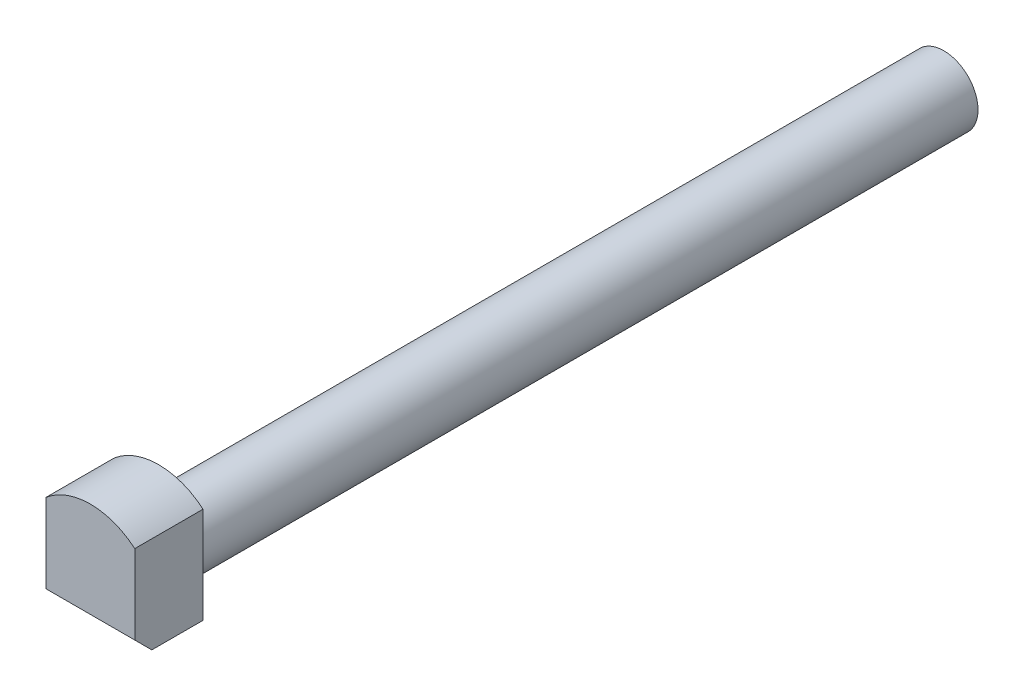
SolidWorks part; units mm, degrees
ref_plane "Plan de face" through (0, 0, 0) normal (0, 0, 1) x (1, 0, 0)
ref_plane "Plan de dessus" through (0, 0, 0) normal (0, 1, 0) x (1, 0, 0)
ref_plane "Plan de droite" through (0, 0, 0) normal (1, 0, 0) x (0, 0, -1)
sketch "Esquisse2" plane through (0, 0, 0) normal (0, 0, 1) x (1, 0, 0)
  circle A0 centre (0, 1.35) radius 1 construction
  circle A1 centre (0, 1.35) radius 1
extrude "Boss.-Extru.1" add sketch "Esquisse2" along normal blind 16.5 and the other way up to surface (11 mm away)
sketch "Esquisse3" plane through (0, 0, 16.5) normal (0, 0, 1) x (1, 0, 0)
  circle A0 centre (0, 1.35) radius 2
  dimension "D1" = 4
extrude "Boss.-Extru.2" add sketch "Esquisse3" along normal blind 2
sketch "Esquisse4" plane through (0, 0, 18.5) normal (0, 0, 1) x (1, 0, 0)
  line L0 (0, 1.35) -> (0, 4.5988) construction
  line L2 (-1.3, 2.8699) -> (-1.3, 0.05)
  line L3 (-1.3, 0.05) -> (1.3, 0.05)
  line L4 (1.3, 2.8699) -> (1.3, 0.05)
  circle A0 centre (0, 1.35) radius 2 construction
  arc A1 (1.3, 2.8699) -> (-1.3, 2.8699) centre (0, 1.35) ccw
  dimension "D1" = 2.6
  dimension "D2" = 1.3
extrude "Enlèv. mat.-Extru.1" cut sketch "Esquisse4" against normal through all flip side to cut
chamfer "Chanfrein1" distance 0.5 angle 45 1 edges at (0, 0.05, 18.5)
sketch "Esquisse6" plane through (0, 0, -11) normal (0, 0, -1) x (-1, 0, 0)
  circle A1 centre (0, 1.35) radius 1
  circle A2 centre (0, 1.35) radius 1
  dimension "D1" = 0
extrude "Enlèv. mat.-Extru.2" cut sketch "Esquisse6" against normal blind 4.5
